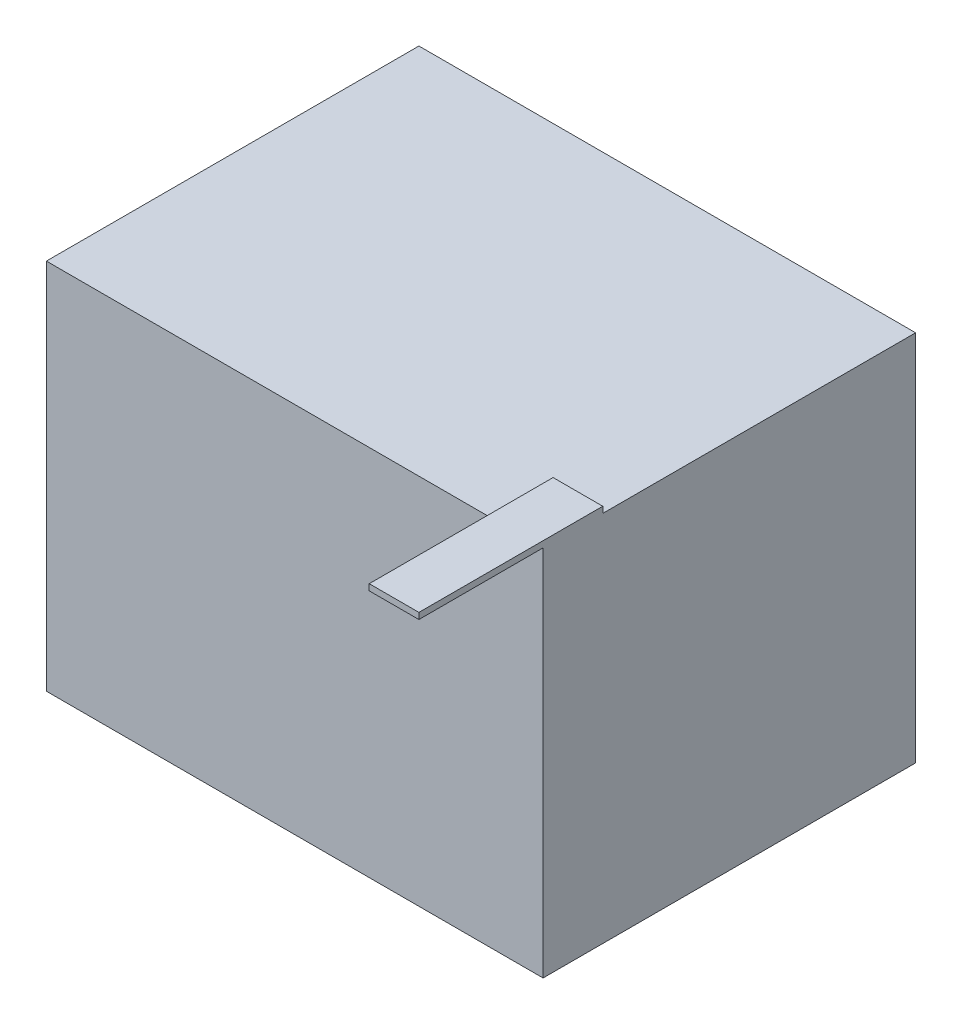
SolidWorks part; units mm, degrees
ref_plane "Front Plane" through (0, 0, 0) normal (0, 0, 1) x (1, 0, 0)
ref_plane "Top Plane" through (0, 0, 0) normal (0, 1, 0) x (1, 0, 0)
ref_plane "Right Plane" through (0, 0, 0) normal (1, 0, 0) x (0, 0, -1)
sketch "Sketch1" plane through (0, 0, 0) normal (0, 1, 0) x (1, 0, 0)
  line L21 (0, 0) -> (800, 0)
  line L22 (0, 0) -> (0, 600)
  line L23 (0, 600) -> (800, 600)
  line L25 (800, 0) -> (800, 600)
  dimension "D1" = 800
  dimension "D2" = 600
extrude "Boss-Extrude1" add sketch "Sketch1" along normal blind 600
sketch "Sketch2" plane through (0, 600, 0) normal (0, 1, 0) x (1, 0, 0)
  line L0 (800, 0) -> (800, 600) construction
  line L1 (800, 96.0954) -> (720, 96.0954)
  line L2 (800, 96.0954) -> (800, -200)
  line L3 (800, -200) -> (720, -200)
  line L4 (720, 96.0954) -> (720, -200)
  dimension "D1" = 80
  dimension "D2" = 800
extrude "Boss-Extrude2" add sketch "Sketch2" along normal blind 10 contours L3 L4 L1 L2
